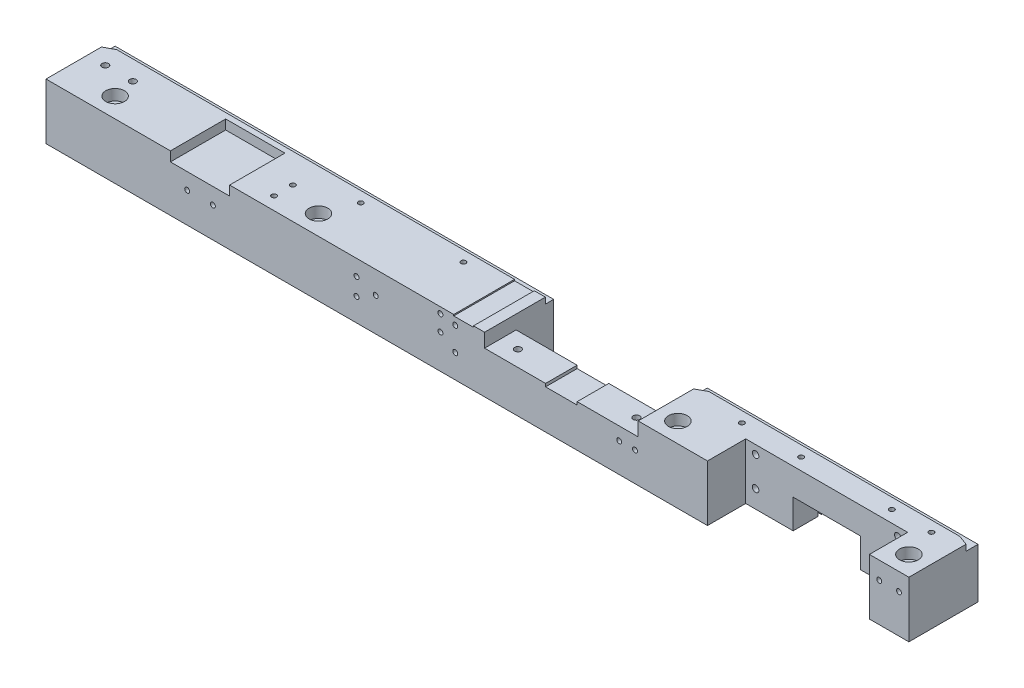
SolidWorks part; units mm, degrees
ref_plane "Front Plane" through (0, 0, 0) normal (0, 0, 1) x (1, 0, 0)
ref_plane "Top Plane" through (0, 0, 0) normal (0, 1, 0) x (1, 0, 0)
ref_plane "Right Plane" through (0, 0, 0) normal (1, 0, 0) x (0, 0, -1)
sketch "Sketch1" plane through (0, 0, 0) normal (0, 0, 1) x (1, 0, 0)
  line L0 (267.0757, 27.9424) -> (311.0757, 27.9424)
  line L1 (-125.9243, 56.2924) -> (96.1757, 56.2924)
  line L2 (-125.9243, 56.2924) -> (-125.9243, 27.9424)
  line L3 (-125.9243, 27.9424) -> (233.0757, 27.9424)
  line L4 (311.0757, 56.2924) -> (311.0757, 27.9424)
  line L5 (173.9757, 56.2924) -> (311.0757, 56.2924)
  line L6 (267.0757, 27.9424) -> (267.0757, 42.7424)
  line L7 (267.0757, 42.7424) -> (233.0757, 42.7424)
  line L8 (233.0757, 27.9424) -> (233.0757, 42.7424)
  line L9 (143.0757, 49.2924) -> (173.9757, 49.2924)
  line L10 (96.1757, 56.2924) -> (96.1757, 49.2924)
  line L11 (96.1757, 49.2924) -> (127.0757, 49.2924)
  line L12 (173.9757, 56.2924) -> (173.9757, 49.2924)
  line L14 (127.0757, 49.2924) -> (127.0757, 47.7857)
  line L15 (127.0757, 47.7857) -> (143.0757, 47.7857)
  line L16 (143.0757, 49.2924) -> (143.0757, 47.7857)
  dimension "D1" = 437
  dimension "D2" = 28.35
  dimension "D3" = 359
  dimension "D4" = 393
  dimension "D5" = 14.8
  dimension "D6" = 222.1
  dimension "D7" = 299.9
  dimension "D8" = 21.35
  dimension "D9" = 253
  dimension "D10" = 269
extrude "Boss-Extrude1" add sketch "Sketch1" along normal blind 35
sketch "Sketch2" plane through (0, 56.2924, 0) normal (0, 1, 0) x (1, 0, 0)
  line L2 (-62.9243, -7) -> (-62.9243, -35)
  line L3 (-62.9243, -35) -> (-32.9243, -35)
  line L4 (-32.9243, -7) -> (-32.9243, -35)
  line L5 (-125.9243, -35) -> (-125.9243, 0) construction
  line L6 (96.1757, -35) -> (-125.9243, -35) construction
  line L7 (-62.9243, -7) -> (-32.9243, -7)
  dimension "D1" = 63
  dimension "D2" = 93
  dimension "D3" = 0
extrude "Cut-Extrude1" cut sketch "Sketch2" against normal blind 4.85
sketch "Sketch3" plane through (0, 49.2924, 0) normal (0, 1, 0) x (1, 0, 0)
  line L0 (96.1757, -35) -> (96.1757, 0) construction
  line L1 (173.9757, 0) -> (96.1757, 0)
  line L2 (173.9757, 0) -> (173.9757, -19)
  line L3 (173.9757, -19) -> (96.1757, -19)
  line L4 (96.1757, 0) -> (96.1757, -19)
  dimension "D1" = 19
extrude "Cut-Extrude2" cut sketch "Sketch3" against normal through all
sketch "Sketch4" plane through (0, 56.2924, 0) normal (0, 1, 0) x (1, 0, 0)
  line L2 (311.0757, 0) -> (173.9757, 0) construction
  line L3 (209.0757, -15.63) -> (291.0757, -15.63)
  line L6 (311.0757, -35) -> (173.9757, -35) construction
  line L8 (209.0757, -15.63) -> (209.0757, -35)
  line L9 (209.0757, -35) -> (291.0757, -35)
  line L10 (291.0757, -35) -> (291.0757, -15.63)
  dimension "D1" = 15.63
extrude "Cut-Extrude3" cut sketch "Sketch4" against normal through all
sketch "Sketch5" plane through (0, 56.2924, 0) normal (0, 1, 0) x (1, 0, 0)
  line L0 (-125.9243, -6.9222) -> (-120.9243, -4.1934)
  line L1 (-125.9243, -35) -> (-125.9243, 0) construction
  line L2 (-120.9243, -4.1934) -> (96.1757, -4.1934)
  line L3 (96.1757, -35) -> (96.1757, 0) construction
  line L4 (-125.9243, 0) -> (311.0757, 0)
  line L5 (311.0757, 0) -> (311.0757, -6.0437)
  line L6 (311.0757, -35) -> (311.0757, 0) construction
  line L7 (311.0757, -6.0437) -> (306.0757, -4.1934)
  line L8 (306.0757, -4.1934) -> (178.9757, -4.1934)
  line L9 (178.9757, -4.1934) -> (173.9757, -6.9222)
  line L10 (173.9757, -35) -> (173.9757, 0) construction
  line L11 (173.9757, -6.9222) -> (173.9757, -4.1934)
  line L12 (173.9757, -4.1934) -> (96.1757, -4.1934)
  line L13 (-125.9243, -6.9222) -> (-125.9243, 0)
  dimension "D1" = 5
  dimension "D2" = 5
  dimension "D3" = 5
extrude "Cut-Extrude5" cut sketch "Sketch5" against normal blind 3.08
sketch "Sketch7" plane through (0, 53.2124, 0) normal (0, 1, 0) x (1, 0, 0)
  line L0 (-125.9243, -35) -> (-125.9243, -6.9222) construction
  line L1 (216.0757, -1.33) -> (284.0757, -1.33)
  line L2 (216.0757, -1.33) -> (216.0757, -2.93)
  line L3 (216.0757, -2.93) -> (284.0757, -2.93)
  line L4 (284.0757, -1.33) -> (284.0757, -2.93)
  line L5 (311.0757, 0) -> (173.9757, 0) construction
  dimension "D1" = 342
  dimension "D2" = 410
  dimension "D3" = 1.33
  dimension "D4" = 1.6
extrude "Cut-Extrude6" cut sketch "Sketch7" against normal through all
sketch "Sketch8" plane through (0, 56.2924, 0) normal (0, 1, 0) x (1, 0, 0)
  line L0 (-125.9243, 0) -> (96.1757, 0) construction
  line L1 (-125.9243, -35) -> (-125.9243, -6.9222) construction
  circle A0 centre (-100.9243, -25) radius 2.75
  circle A1 centre (2.0757, -25) radius 2.75
  circle A2 centre (184.0757, -25) radius 2.75
  circle A3 centre (301.0757, -25) radius 2.75
  point P8 (0, 0)
  dimension "D1" = 5.5
  dimension "D2" = 25
  dimension "D3" = 25
  dimension "D4" = 128
  dimension "D5" = 310
  dimension "D6" = 427
extrude "Cut-Extrude7" cut sketch "Sketch8" against normal through all
sketch "Sketch9" plane through (0, 56.2924, 0) normal (0, 1, 0) x (1, 0, 0)
  circle A0 centre (-100.9243, -25) radius 4.75
  circle A1 centre (2.0757, -25) radius 4.75
  circle A2 centre (184.0757, -25) radius 4.75
  circle A3 centre (301.0757, -25) radius 4.75
  dimension "D1" = 9.5
extrude "Cut-Extrude8" cut sketch "Sketch9" against normal blind 5.5
hole_wizard "M4 Tapped Hole1" positions "Sketch10" profile "Sketch11" tap size "M4" standard "ISO"
sketch "Sketch10" plane through (0, 56.2924, 0) normal (0, 1, 0) x (1, 0, 0)
  line L0 (-125.9243, -35) -> (-125.9243, -6.9222) construction
  line L1 (-125.9243, 0) -> (96.1757, 0) construction
  point P0 (-116.9243, -14)
  point P2 (-102.9243, -14)
  dimension "D1" = 9
  dimension "D2" = 23
  dimension "D3" = 14
  dimension "D4" = 14
sketch "Sketch11" plane through (-116.9243, 56.2924, 14) normal (1, 0, 0) x (0, 0, 1)
  line L0 (0, 0) -> (0, 8.9914)
  line L1 (0, 8.9914) -> (1.65, 8)
  line L2 (1.65, 8) -> (1.65, 0)
  line L5 (1.65, 0) -> (0, 0)
  line L10 (0, 8.9914) -> (-1.65, 8) construction
  line L11 (0, -6.35) -> (0, 107.95) construction
  dimension "Tap Drill Dia." = 3.3
  dimension "Tap Drill Depth" = 8
  dimension "Drill Angle" = 118
cosmetic thread "Hole Thread1" parameters "D1"=8, "D2"=4
cosmetic thread "Hole Thread2" parameters "D1"=8, "D2"=4
hole_wizard "M4 Tapped Hole2" positions "Sketch12" profile "Sketch13" tap size "M4" standard "ISO"
sketch "Sketch12" plane through (0, 49.2924, 0) normal (0, 1, 0) x (1, 0, 0)
  line L0 (-125.9243, -35) -> (-125.9243, -6.9222) construction
  line L1 (-125.9243, 0) -> (96.1757, 0) construction
  line L2 (311.0757, 0) -> (173.9757, 0) construction
  point P0 (105.0757, -27)
  point P2 (165.0757, -27)
  dimension "D1" = 231
  dimension "D2" = 291
  dimension "D3" = 27
  dimension "D4" = 27
sketch "Sketch13" plane through (105.0757, 49.2924, 27) normal (1, 0, 0) x (0, 0, 1)
  line L0 (0, 0) -> (0, 8.9914)
  line L1 (0, 8.9914) -> (1.65, 8)
  line L2 (1.65, 8) -> (1.65, 0)
  line L5 (1.65, 0) -> (0, 0)
  line L10 (0, 8.9914) -> (-1.65, 8) construction
  line L11 (0, -6.35) -> (0, 107.95) construction
  dimension "Tap Drill Dia." = 3.3
  dimension "Tap Drill Depth" = 8
  dimension "Drill Angle" = 118
cosmetic thread "Hole Thread3" parameters "D1"=8, "D2"=4
cosmetic thread "Hole Thread4" parameters "D1"=8, "D2"=4
hole_wizard "M3 Tapped Hole1" positions "Sketch14" profile "Sketch15" tap size "M3" standard "ISO"
sketch "Sketch14" plane through (0, 56.2924, 0) normal (0, 1, 0) x (1, 0, 0)
  line L0 (-125.9243, -35) -> (-125.9243, -6.9222) construction
  line L1 (-125.9243, 0) -> (96.1757, 0) construction
  point P0 (-16.9243, -19)
  point P2 (-16.9243, -28.5)
  point P4 (8.0757, -9.6)
  point P6 (60.0757, -9.6)
  point P8 (201.0757, -9.6)
  point P10 (231.0757, -9.6)
  point P12 (277.0757, -9.6)
  point P14 (297.0757, -9.6)
  point P21 (0, 0)
  dimension "D1" = 109
  dimension "D2" = 109
  dimension "D3" = 28.5
  dimension "D4" = 19
  dimension "D5" = 134
  dimension "D6" = 186
  dimension "D7" = 9.6
  dimension "D8" = 327
  dimension "D9" = 30
  dimension "D10" = 403
  dimension "D11" = 423
sketch "Sketch15" plane through (-16.9243, 56.2924, 19) normal (1, 0, 0) x (0, 0, 1)
  line L0 (0, 0) -> (0, 6.7511)
  line L1 (0, 6.7511) -> (1.25, 6)
  line L2 (1.25, 6) -> (1.25, 0)
  line L5 (1.25, 0) -> (0, 0)
  line L10 (0, 6.7511) -> (-1.25, 6) construction
  line L11 (0, -6.35) -> (0, 107.95) construction
  dimension "Tap Drill Dia." = 2.5
  dimension "Tap Drill Depth" = 6
  dimension "Drill Angle" = 118
cosmetic thread "Hole Thread5" parameters "D1"=6, "D2"=3
cosmetic thread "Hole Thread6" parameters "D1"=6, "D2"=3
cosmetic thread "Hole Thread7" parameters "D1"=6, "D2"=3
cosmetic thread "Hole Thread8" parameters "D1"=6, "D2"=3
cosmetic thread "Hole Thread9" parameters "D1"=6, "D2"=3
cosmetic thread "Hole Thread10" parameters "D1"=6, "D2"=3
cosmetic thread "Hole Thread11" parameters "D1"=6, "D2"=3
cosmetic thread "Hole Thread12" parameters "D1"=6, "D2"=3
hole_wizard "M3 Tapped Hole2" positions "Sketch16" profile "Sketch17" tap size "M3" standard "ISO"
sketch "Sketch16" plane through (0, 0, 35) normal (0, 0, 1) x (1, 0, 0)
  line L0 (-125.9243, 56.2924) -> (-125.9243, 27.9424) construction
  line L1 (-62.9243, 56.2924) -> (-125.9243, 56.2924) construction
  line L2 (-125.9243, 27.9424) -> (209.0757, 27.9424) construction
  line L3 (291.0757, 27.9424) -> (311.0757, 27.9424) construction
  point P0 (-54.4243, 43.2924)
  point P2 (-41.4243, 43.2924)
  point P4 (31.3257, 48.3077)
  point P6 (31.3257, 39.5626)
  point P8 (41.0757, 44.895)
  point P10 (81.3257, 51.9424)
  point P12 (81.3257, 39.9424)
  point P16 (164.3757, 42.7424)
  point P18 (172.3757, 42.7424)
  point P20 (296.0757, 47.4424)
  point P22 (306.0757, 47.4424)
  point P33 (0, 0)
  dimension "D1" = 71.5
  dimension "D2" = 84.5
  dimension "D3" = 13
  dimension "D4" = 13
  dimension "D5" = 157.25
  dimension "D6" = 157.25
  dimension "D7" = 167
  dimension "D8" = 290.3
  dimension "D9" = 298.3
  dimension "D10" = 14.8
  dimension "D11" = 14.8
  dimension "D12" = 422
  dimension "D13" = 432
  dimension "D14" = 19.5
  dimension "D15" = 19.5
  dimension "D16" = 207.25
  dimension "D17" = 207.25
  dimension "D18" = 12
  dimension "D19" = 24
sketch "Sketch17" plane through (-54.4243, 43.2924, 35) normal (1, 0, 0) x (0, -1, 0)
  line L0 (0, 0) -> (0, 6.7511)
  line L1 (0, 6.7511) -> (1.25, 6)
  line L2 (1.25, 6) -> (1.25, 0)
  line L5 (1.25, 0) -> (0, 0)
  line L10 (0, 6.7511) -> (-1.25, 6) construction
  line L11 (0, -6.35) -> (0, 107.95) construction
  dimension "Tap Drill Dia." = 2.5
  dimension "Tap Drill Depth" = 6
  dimension "Drill Angle" = 118
cosmetic thread "Hole Thread13" parameters "D1"=6, "D2"=3
cosmetic thread "Hole Thread14" parameters "D1"=6, "D2"=3
cosmetic thread "Hole Thread15" parameters "D1"=6, "D2"=3
cosmetic thread "Hole Thread16" parameters "D1"=6, "D2"=3
cosmetic thread "Hole Thread18" parameters "D1"=6, "D2"=3
cosmetic thread "Hole Thread19" parameters "D1"=6, "D2"=3
cosmetic thread "Hole Thread20" parameters "D1"=6, "D2"=3
cosmetic thread "Hole Thread21" parameters "D1"=6, "D2"=3
cosmetic thread "Hole Thread22" parameters "D1"=6, "D2"=3
cosmetic thread "Hole Thread23" parameters "D1"=6, "D2"=3
cosmetic thread "Hole Thread24" parameters "D1"=6, "D2"=3
hole_wizard "M3 Tapped Hole3" positions "Sketch18" profile "Sketch19" tap size "M3" standard "ISO"
sketch "Sketch18" plane through (0, 0, 35) normal (0, 0, 1) x (1, 0, 0)
  line L0 (-125.9243, 27.9424) -> (209.0757, 27.9424) construction
  point P0 (73.8225, 53.2124)
  point P2 (73.8225, 45.2124)
  dimension "D1" = 25.27
  dimension "D2" = 17.27
sketch "Sketch19" plane through (73.8225, 53.2124, 35) normal (1, 0, 0) x (0, -1, 0)
  line L0 (0, 0) -> (0, 6.7511)
  line L1 (0, 6.7511) -> (1.25, 6)
  line L2 (1.25, 6) -> (1.25, 0)
  line L5 (1.25, 0) -> (0, 0)
  line L10 (0, 6.7511) -> (-1.25, 6) construction
  line L11 (0, -6.35) -> (0, 107.95) construction
  dimension "Tap Drill Dia." = 2.5
  dimension "Tap Drill Depth" = 6
  dimension "Drill Angle" = 118
cosmetic thread "Hole Thread25" parameters "D1"=6, "D2"=3
cosmetic thread "Hole Thread26" parameters "D1"=6, "D2"=3
hole_wizard "M4 Tapped Hole3" positions "Sketch20" profile "Sketch21" tap size "M4" standard "ISO"
sketch "Sketch20" plane through (0, 0, 15.63) normal (0, 0, 1) x (1, 0, 0)
  line L0 (-125.9243, 56.2924) -> (-125.9243, 27.9424) construction
  line L1 (233.0757, 27.9424) -> (209.0757, 27.9424) construction
  line L2 (291.0757, 27.9424) -> (267.0757, 27.9424) construction
  point P0 (214.0757, 51.9424)
  point P2 (214.0757, 36.9424)
  point P4 (286.0757, 36.9424)
  point P6 (286.0757, 51.9424)
  dimension "D1" = 340
  dimension "D2" = 340
  dimension "D3" = 412
  dimension "D4" = 412
  dimension "D5" = 24
  dimension "D6" = 9
  dimension "D7" = 9
  dimension "D8" = 24
sketch "Sketch21" plane through (214.0757, 51.9424, 15.63) normal (1, 0, 0) x (0, -1, 0)
  line L0 (0, 0) -> (0, 8.9914)
  line L1 (0, 8.9914) -> (1.65, 8)
  line L2 (1.65, 8) -> (1.65, 0)
  line L5 (1.65, 0) -> (0, 0)
  line L10 (0, 8.9914) -> (-1.65, 8) construction
  line L11 (0, -6.35) -> (0, 107.95) construction
  dimension "Tap Drill Dia." = 3.3
  dimension "Tap Drill Depth" = 8
  dimension "Drill Angle" = 118
cosmetic thread "Hole Thread27" parameters "D1"=8, "D2"=4
cosmetic thread "Hole Thread28" parameters "D1"=8, "D2"=4
cosmetic thread "Hole Thread29" parameters "D1"=8, "D2"=4
cosmetic thread "Hole Thread30" parameters "D1"=8, "D2"=4
sketch "Sketch22" plane through (0, 56.2924, 0) normal (0, 1, 0) x (1, 0, 0)
  line L0 (96.1757, -35) -> (-32.9243, -35) construction
  line L1 (80.5757, -35) -> (90.5757, -35)
  line L2 (80.5757, -35) -> (80.5757, -4.1934)
  line L3 (80.5757, -4.1934) -> (90.5757, -4.1934)
  line L4 (90.5757, -35) -> (90.5757, -4.1934)
  line L5 (-120.9243, -4.1934) -> (96.1757, -4.1934) construction
  line L6 (-125.9243, -35) -> (-125.9243, -6.9222) construction
  dimension "D1" = 206.5
  dimension "D2" = 10
extrude "Cut-Extrude9" cut sketch "Sketch22" against normal blind 0.65
